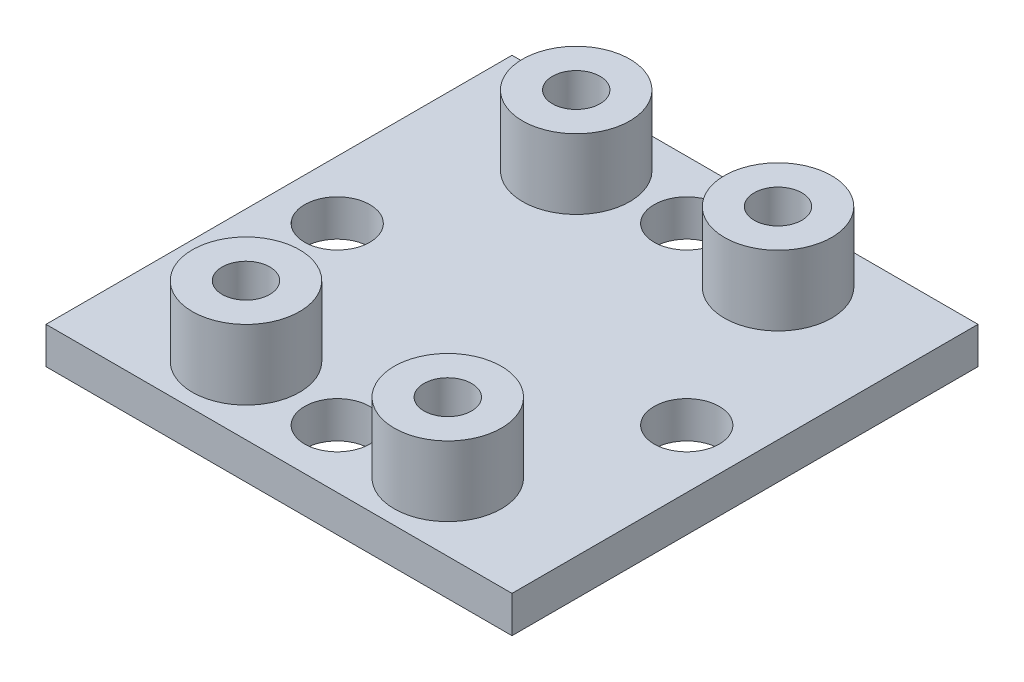
SolidWorks part; units mm, degrees
ref_plane "Front Plane" through (0, 0, 0) normal (0, 0, 1) x (1, 0, 0)
ref_plane "Top Plane" through (0, 0, 0) normal (0, 1, 0) x (1, 0, 0)
ref_plane "Right Plane" through (0, 0, 0) normal (1, 0, 0) x (0, 0, -1)
sketch "Sketch1" plane through (0, 0, 0) normal (0, 1, 0) x (1, 0, 0)
  line L0 (-12.7, -12.7) -> (12.7, 12.7) construction
  line L1 (-12.7, 12.7) -> (12.7, 12.7)
  line L2 (-12.7, 12.7) -> (-12.7, -12.7)
  line L3 (-12.7, -12.7) -> (12.7, -12.7)
  line L4 (12.7, 12.7) -> (12.7, -12.7)
  point P4 (0, 0)
  dimension "D1" = 25.4
  dimension "D2" = 25.4
extrude "Boss-Extrude1" add sketch "Sketch1" along normal blind 2
sketch "Sketch3" plane through (0, 2, 0) normal (0, 1, 0) x (1, 0, 0)
  line L0 (-5.5, -9) -> (5.5, -9) construction
  line L1 (5.5, -9) -> (5.5, 9) construction
  line L2 (5.5, 9) -> (-5.5, 9) construction
  line L3 (-5.5, 9) -> (-5.5, -9) construction
  line L4 (-5.5, -9) -> (5.5, 9) construction
  circle A0 centre (-5.5, -9) radius 1.3
  circle A1 centre (5.5, 9) radius 1.3
  circle A2 centre (-5.5, 9) radius 1.3
  circle A3 centre (5.5, -9) radius 1.3
  circle A4 centre (-5.5, 9) radius 2.921
  circle A5 centre (5.5, 9) radius 2.921
  circle A6 centre (5.5, -9) radius 2.921
  circle A7 centre (-5.5, -9) radius 2.921
  point P2 (0, 0)
  dimension "D1" = 2.6
  dimension "D4" = 5.842
  dimension "D2" = 11
  dimension "D3" = 18
sketch "Sketch4" plane through (0, 0, 0) normal (0, 1, 0) x (1, 0, 0)
  line L0 (-12.7, 0) -> (12.7, 0) construction
  line L1 (-12.7, 12.7) -> (-12.7, -12.7) construction
  line L2 (12.7, -12.7) -> (12.7, 12.7) construction
  circle A0 centre (0, 0) radius 6.35 construction
  circle A1 centre (-9.525, 0) radius 1.778
  point P10 (0, 0)
  point P14 (-9.779, 0)
  dimension "D1" = 12.7
  dimension "D2" = 3.556
  dimension "D4" = 9.525
extrude "Cut-Extrude1" cut sketch "Sketch4" along normal through all
sketch "Sketch5" plane through (0, 0, 0) normal (1, 0, 0) x (0, 0, -1)
  line L0 (0, 0) -> (0, 6.6753) construction
  point P3 (0, 0)
  dimension "D1" = 6.6753
extrude "Boss-Extrude2" add sketch "Sketch3" along normal blind 3.81
pattern_circular "CirPattern2" count 4 over 360 about axis through (0, 0, 0) along (0, 1, 0) of "Cut-Extrude1"
